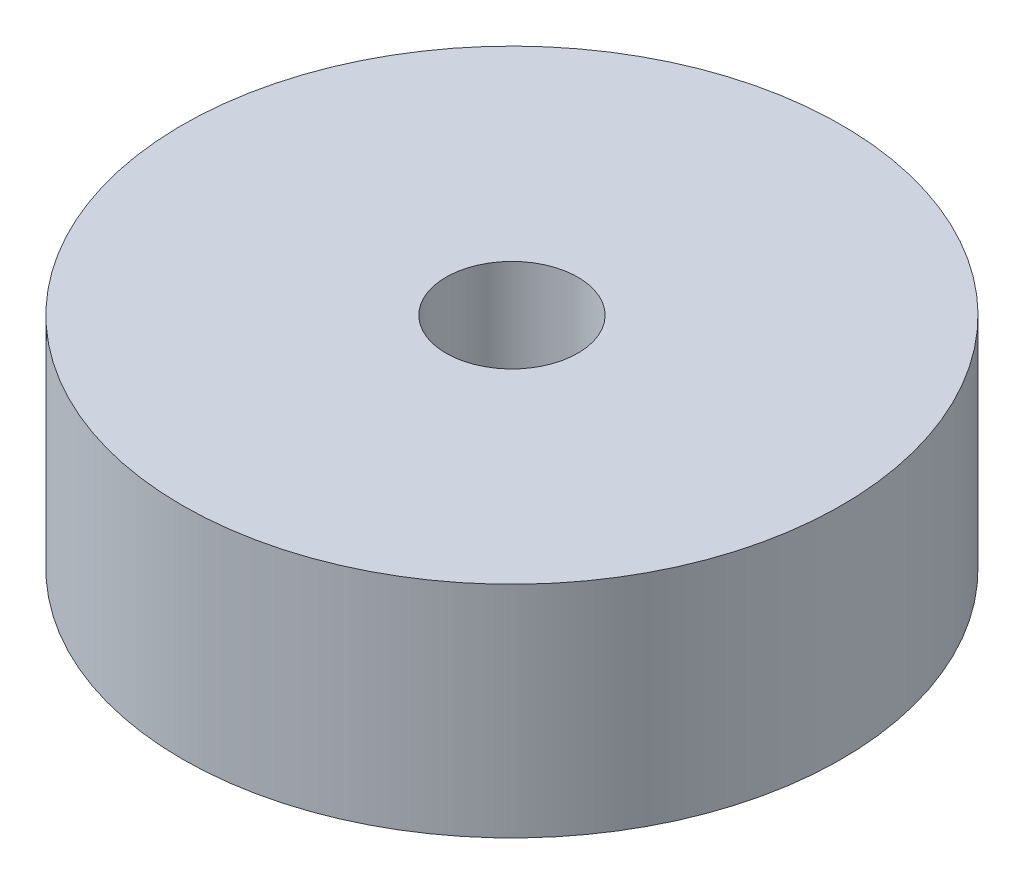
SolidWorks part; units mm, degrees
ref_plane "前视基准面" through (0, 0, 0) normal (0, 0, 1) x (1, 0, 0)
ref_plane "上视基准面" through (0, 0, 0) normal (0, 1, 0) x (1, 0, 0)
ref_plane "右视基准面" through (0, 0, 0) normal (1, 0, 0) x (0, 0, -1)
sketch "草图1" plane through (0, 0, 0) normal (0, 1, 0) x (1, 0, 0)
  circle A0 centre (0, 0) radius 15
  circle A1 centre (0, 0) radius 3
  dimension "D1" = 30
extrude "凸台-拉伸1" add sketch "草图1" along normal blind 10
